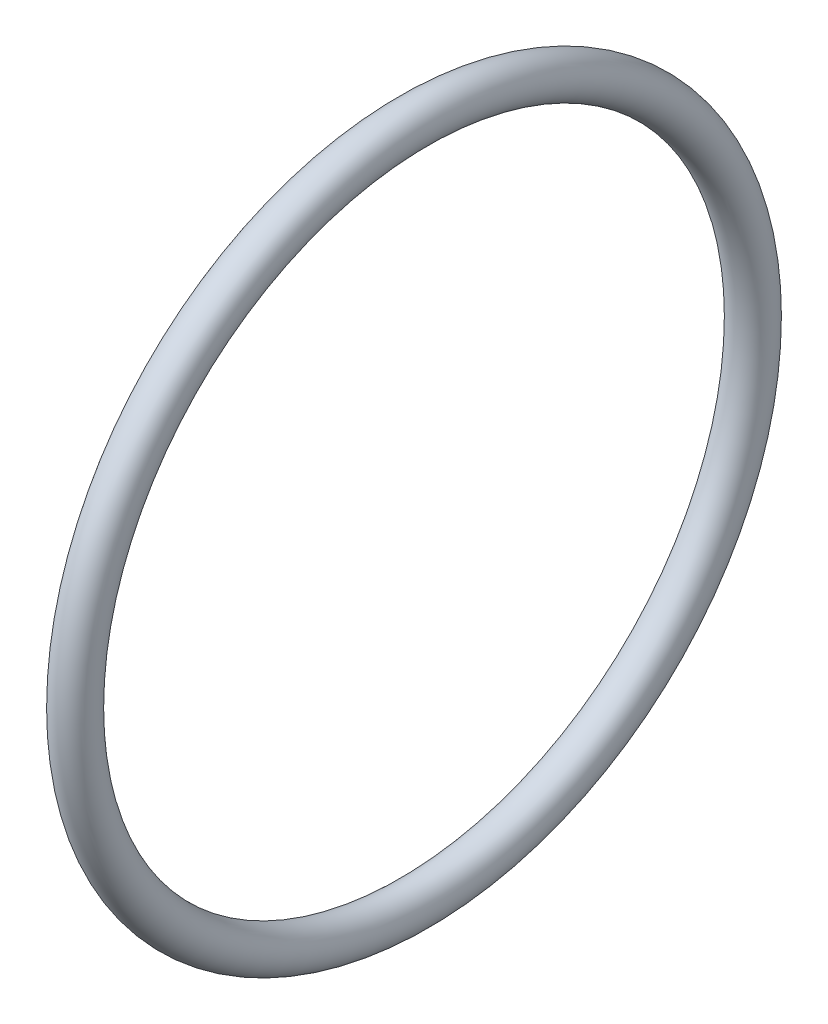
SolidWorks part; units mm, degrees
ref_plane "Front Plane" through (0, 0, 0) normal (0, 0, 1) x (1, 0, 0)
ref_plane "Top Plane" through (0, 0, 0) normal (0, 1, 0) x (1, 0, 0)
ref_plane "Right Plane" through (0, 0, 0) normal (1, 0, 0) x (0, 0, -1)
sketch "Sketch2" plane through (0, 0, 0) normal (0, 0, 1) x (1, 0, 0)
  line L0 (0, 0) -> (58.591, 0) construction
  line L2 (0, 0) -> (18.4, 0)
  line L3 (0, 0) -> (0, 2.5)
  line L4 (0, 2.5) -> (18.4, 2.5)
  line L5 (18.4, 0) -> (18.4, 2.5)
  line L6 (6.0094, 2.5) -> (6.0094, 6)
  line L11 (6.0094, 6) -> (9.9794, 6)
  line L16 (12.9794, 6) -> (12.9794, 3)
  line L17 (12.9794, 3) -> (13.6398, 3)
  line L18 (13.6398, 3) -> (13.6398, 2.5)
  line L19 (13.6398, 2.5) -> (6.0094, 2.5)
  line L22 (13.6398, 2.5) -> (16.1198, 2.5)
  line L23 (13.6398, 2.5) -> (13.6398, 4)
  line L24 (13.6398, 4) -> (16.1198, 4)
  line L25 (16.1198, 2.5) -> (16.1198, 4)
  line L27 (6.0094, 6) -> (9.9794, 6)
  line L28 (6.0094, 6) -> (6.0094, 9)
  line L29 (6.0094, 9) -> (9.9794, 9)
  line L30 (9.9794, 6) -> (9.9794, 9)
  line L31 (6.0094, 9) -> (6.0094, 8.25)
  line L32 (6.0094, 8.25) -> (5.0094, 8.25)
  line L33 (8.6609, 22.001) -> (8.6609, 12.476) construction
  line L34 (5.0094, 12.476) -> (12.3124, 12.476)
  line L35 (9.9794, 9) -> (12.3124, 9)
  line L36 (5.0094, 7.9375) -> (1.7709, 7.9375)
  line L37 (5.0094, 8.25) -> (5.0094, 12.476)
  line L38 (5.0094, 7.9375) -> (5.0094, 13.9365)
  line L39 (5.0094, 13.9365) -> (1.7709, 13.9365)
  line L40 (1.7709, 7.9375) -> (1.7709, 13.9365)
  line L41 (5.0094, 22.001) -> (12.3124, 22.001)
  line L42 (5.0094, 22.001) -> (5.0094, 30.1625)
  line L43 (5.0094, 30.1625) -> (12.3124, 30.1625)
  line L44 (12.3124, 22.001) -> (12.3124, 30.1625)
  line L49 (16.6398, 22.001) -> (16.6398, 7.5)
  line L51 (23.0198, 7.5) -> (23.0198, 6.5)
  line L54 (16.1198, 4) -> (13.6398, 4)
  line L56 (18.0398, 7.5) -> (23.0198, 7.5)
  line L57 (13.3124, 22.001) -> (16.6398, 22.001)
  line L58 (16.1198, 3.5) -> (20.0198, 3.5)
  line L59 (29.9098, 14) -> (26.9098, 11)
  line L60 (4.0094, 31.75) -> (18.0398, 31.75)
  line L61 (18.0398, 7.5) -> (23.0198, 7.5)
  line L62 (18.0398, 7.5) -> (18.0398, 12)
  line L63 (18.0398, 12) -> (23.0198, 12)
  line L64 (23.0198, 7.5) -> (23.0198, 12)
  line L65 (18.0398, 31.75) -> (18.0398, 12)
  line L66 (23.0198, 11) -> (26.9098, 11)
  line L67 (34.8098, 23) -> (31.3098, 19.5)
  line L68 (35.8098, 31) -> (38.7998, 33.99)
  line L69 (29.9098, 14) -> (29.9098, 15)
  line L70 (29.9098, 15) -> (22.9398, 15)
  line L71 (22.9398, 15) -> (21.0398, 15)
  line L72 (18.0398, 7.5) -> (16.6398, 7.5)
  line L73 (21.0398, 15) -> (21.0398, 43)
  line L74 (19.6115, 40) -> (9.6516, 40)
  line L75 (9.6516, 40) -> (4.0094, 40)
  line L76 (21.0398, 43) -> (19.6115, 43)
  line L77 (22.9398, 15) -> (29.9098, 15)
  line L78 (22.9398, 15) -> (22.9398, 21)
  line L79 (22.9398, 21) -> (29.9098, 21)
  line L80 (29.9098, 15) -> (29.9098, 21)
  line L81 (9.6516, 40) -> (19.6115, 40)
  line L82 (9.6516, 40) -> (9.6516, 50)
  line L83 (9.6516, 50) -> (19.6115, 50)
  line L84 (19.6115, 40) -> (19.6115, 50)
  line L85 (4.0094, 40) -> (4.0094, 31.75)
  line L86 (12.9794, 3) -> (12.9794, 2.5)
  line L87 (31.3098, 19.5) -> (29.9098, 19.5)
  line L88 (21.4694, 63.5) -> (21.4694, 51.308)
  line L89 (21.4694, 63.5) -> (25.9398, 63.5)
  line L90 (25.9398, 63.5) -> (25.9398, 25)
  line L91 (27.8398, 25) -> (25.9398, 25)
  line L92 (9.6516, 48) -> (8.2233, 48)
  line L93 (8.2233, 48) -> (8.2233, 53.476)
  line L94 (8.2233, 53.476) -> (19.6115, 53.476)
  line L95 (19.6115, 53.476) -> (19.6115, 50)
  line L96 (13.9174, 63.001) -> (13.9174, 53.476) construction
  line L97 (8.2233, 63.001) -> (19.6115, 63.001)
  line L98 (8.2233, 63.001) -> (8.2233, 68.2625)
  line L99 (8.2233, 68.2625) -> (19.6115, 68.2625)
  line L100 (19.6115, 63.001) -> (19.6115, 68.2625)
  line L101 (12.9794, 6) -> (11.9794, 6)
  line L102 (8.2233, 44.825) -> (4.9848, 44.825)
  line L103 (8.2233, 44.825) -> (8.2233, 54.9365)
  line L104 (8.2233, 54.9365) -> (4.9848, 54.9365)
  line L106 (9.9794, 6) -> (10.8794, 6)
  line L107 (27.8398, 25) -> (34.8098, 25)
  line L108 (34.8098, 25) -> (34.8098, 23)
  line L109 (0, 0) -> (-2, 0)
  line L110 (0, 0) -> (0, 11)
  line L111 (27.8398, 25) -> (34.8098, 25)
  line L112 (27.8398, 25) -> (27.8398, 32.5)
  line L113 (27.8398, 32.5) -> (34.8098, 32.5)
  line L114 (34.8098, 25) -> (34.8098, 32.5)
  line L115 (35.8098, 31) -> (34.8098, 31)
  line L116 (27.8398, 32.5) -> (27.8398, 64.5)
  line L117 (20.5849, 74.025) -> (6.2499, 74.025)
  line L118 (6.2499, 74.025) -> (6.2499, 76.2)
  line L119 (38.7998, 47.29) -> (30.8398, 55.25)
  line L120 (0, 11) -> (-2, 11)
  line L121 (38.7998, 43.815) -> (30.8623, 43.815)
  line L123 (-4.8152, 69.85) -> (1.5348, 76.2)
  line L124 (38.7998, 47.29) -> (38.7998, 33.99)
  line L125 (-2, 0) -> (-2, 11)
  line L126 (38.7998, 37.465) -> (30.8623, 37.465)
  line L127 (30.8623, 43.815) -> (30.8623, 37.465)
  line L128 (6.0094, 2.5) -> (6.0094, 0)
  line L129 (-0.0152, 63.5) -> (-0.0152, 30)
  line L132 (4.9848, 63.5) -> (-0.0152, 63.5)
  line L136 (-1.8152, 30) -> (-11.7752, 30)
  line L138 (-13.7752, 25.4) -> (-2, 25.4)
  line L139 (-2, 25.4) -> (-2, 11.5)
  line L140 (27.8398, 64.5) -> (20.5849, 64.5)
  line L141 (-1.8152, 30) -> (-11.7752, 30)
  line L142 (-1.8152, 30) -> (-1.8152, 39)
  line L143 (-1.8152, 39) -> (-11.7752, 39)
  line L144 (-11.7752, 30) -> (-11.7752, 39)
  line L145 (20.5849, 64.5) -> (20.5849, 74.025)
  line L146 (-12.7752, 37) -> (-12.7752, 47.29)
  line L147 (-12.7752, 37) -> (-11.7752, 37)
  line L148 (30.8398, 55.25) -> (30.8398, 76.2)
  line L149 (11.9794, 6) -> (11.9794, 5.45)
  line L154 (-2, 11.5) -> (0.5, 11.5)
  line L155 (4.9848, 60.6197) -> (24.0348, 60.6197)
  line L160 (4.9848, 60.6197) -> (4.9848, 55.8572)
  line L161 (4.9848, 55.8572) -> (24.0348, 55.8572)
  line L166 (24.0348, 60.6197) -> (24.0348, 55.8572)
  line L167 (4.9848, 60.6197) -> (24.0348, 55.8572) construction
  line L172 (4.9848, 55.8572) -> (24.0348, 60.6197) construction
  line L173 (24.0348, 62.2072) -> (25.9398, 62.2072)
  line L174 (11.9794, 5.45) -> (10.8794, 5.45)
  line L175 (10.8794, 6) -> (10.8794, 5.45)
  line L176 (24.0348, 62.2072) -> (24.0348, 54.2697)
  line L177 (24.0348, 54.2697) -> (25.9398, 54.2697)
  line L178 (25.9398, 62.2072) -> (25.9398, 54.2697)
  line L179 (24.0348, 62.2072) -> (25.9398, 54.2697) construction
  line L180 (24.0348, 54.2697) -> (25.9398, 62.2072) construction
  line L181 (3, 19.6197) -> (15.7, 19.6197)
  line L182 (3, 19.6197) -> (3, 14.8572)
  line L183 (3, 14.8572) -> (15.7, 14.8572)
  line L184 (15.7, 19.6197) -> (15.7, 14.8572)
  line L185 (3, 19.6197) -> (15.7, 14.8572) construction
  line L186 (3, 14.8572) -> (15.7, 19.6197) construction
  line L187 (15.7, 21.2072) -> (16.6398, 21.2072)
  line L188 (15.7, 21.2072) -> (15.7, 13.2697)
  line L189 (15.7, 13.2697) -> (16.6398, 13.2697)
  line L190 (16.6398, 21.2072) -> (16.6398, 13.2697)
  line L191 (15.7, 21.2072) -> (16.6398, 13.2697) construction
  line L192 (15.7, 13.2697) -> (16.6398, 21.2072) construction
  line L193 (0.5, 11.5) -> (0.5, 6.9375)
  line L194 (0.5, 6.9375) -> (1.7709, 6.9375)
  line L195 (23.0198, 6.5) -> (20.0198, 3.5)
  line L196 (4.9848, 63.5) -> (4.9848, 54.9365)
  line L197 (3, 43.825) -> (4.9848, 43.825)
  line L198 (1.7709, 6.9375) -> (1.7709, 7.9375)
  line L199 (6.0094, 0) -> (12.9794, 0)
  line L200 (12.9794, 0) -> (12.9794, 2.5)
  line L201 (18.0398, 31.75) -> (18.0398, 35.875)
  line L202 (18.0398, 35.875) -> (21.0398, 35.875)
  line L203 (30.8398, 76.2) -> (6.2499, 76.2)
  line L204 (2.8049, 69.85) -> (7.2499, 69.85) construction
  line L205 (7.2499, 67.4688) -> (26.2999, 67.4688)
  line L206 (7.2499, 74.025) -> (7.2499, 64.5)
  line L207 (7.2499, 64.5) -> (-1.8152, 64.5)
  line L208 (-1.8152, 64.5) -> (-1.8152, 39)
  line L209 (-12.7752, 47.29) -> (-4.8152, 55.25)
  line L210 (-4.8152, 55.25) -> (-4.8152, 69.85)
  line L211 (7.2499, 67.4688) -> (7.2499, 72.2312)
  line L212 (7.2499, 72.2312) -> (26.2999, 72.2313)
  line L213 (26.2999, 67.4688) -> (26.2999, 72.2313)
  line L214 (26.2999, 73.8187) -> (30.8398, 73.8187)
  line L215 (26.2999, 73.8187) -> (26.2999, 65.8813)
  line L216 (26.2999, 65.8813) -> (30.8398, 65.8813)
  line L217 (30.8398, 73.8187) -> (30.8398, 65.8813)
  line L218 (2.8049, 72.2313) -> (25.0299, 72.2313)
  line L219 (2.8049, 72.2313) -> (2.8049, 67.4687)
  line L220 (2.8049, 67.4687) -> (25.0299, 67.4687)
  line L221 (25.0299, 72.2313) -> (25.0299, 67.4687)
  line L222 (25.0299, 69.85) -> (20.5849, 69.85) construction
  line L223 (21.4694, 51.308) -> (22.9398, 51.308)
  line L224 (22.9398, 51.308) -> (22.9398, 21)
  line L225 (13.6398, 4) -> (13.6398, 12.2697)
  line L226 (13.6398, 12.2697) -> (13.3124, 12.2697)
  line L227 (13.3124, 12.2697) -> (13.3124, 22.001)
  line L228 (12.3124, 9) -> (12.3124, 12.476)
  line L229 (-1.8152, 30) -> (-0.0152, 30)
  line L230 (8.2233, 65.6317) -> (2.8049, 65.6317) construction
  line L231 (19.6115, 65.6317) -> (25.0299, 65.6317) construction
  line L232 (1.5348, 76.2) -> (6.2499, 76.2)
  line L233 (-11.7752, 30) -> (-13.7752, 30)
  line L234 (-13.7752, 30) -> (-13.7752, 25.4)
  line L235 (3, 13.9365) -> (3, 43.825)
  line L236 (4.9848, 54.9365) -> (4.9848, 44.825)
  line L237 (4.9848, 43.825) -> (4.9848, 44.825)
  circle A0 centre (26.8898, 25.95) radius 0.95
  circle A1 centre (21.9898, 15.95) radius 0.95
  circle A2 centre (17.3398, 8.2) radius 0.7
  circle A3 centre (10.4294, 6.45) radius 0.45
  circle A4 centre (-0.9152, 30.9) radius 0.9
  point P7 (24.9873, 58.2385)
  point P131 (16.1699, 17.2385)
  point P135 (14.5098, 58.2385)
  point P146 (9.35, 17.2385)
sketch "Sketch3" plane through (0, 0, 0) normal (0, 0, 1) x (1, 0, 0)
  circle A0 centre (21.9898, 15.95) radius 0.95 construction
  circle A1 centre (21.9898, 15.95) radius 0.95
revolve "Revolve1" add sketch "Sketch3" angle 360 about L0
